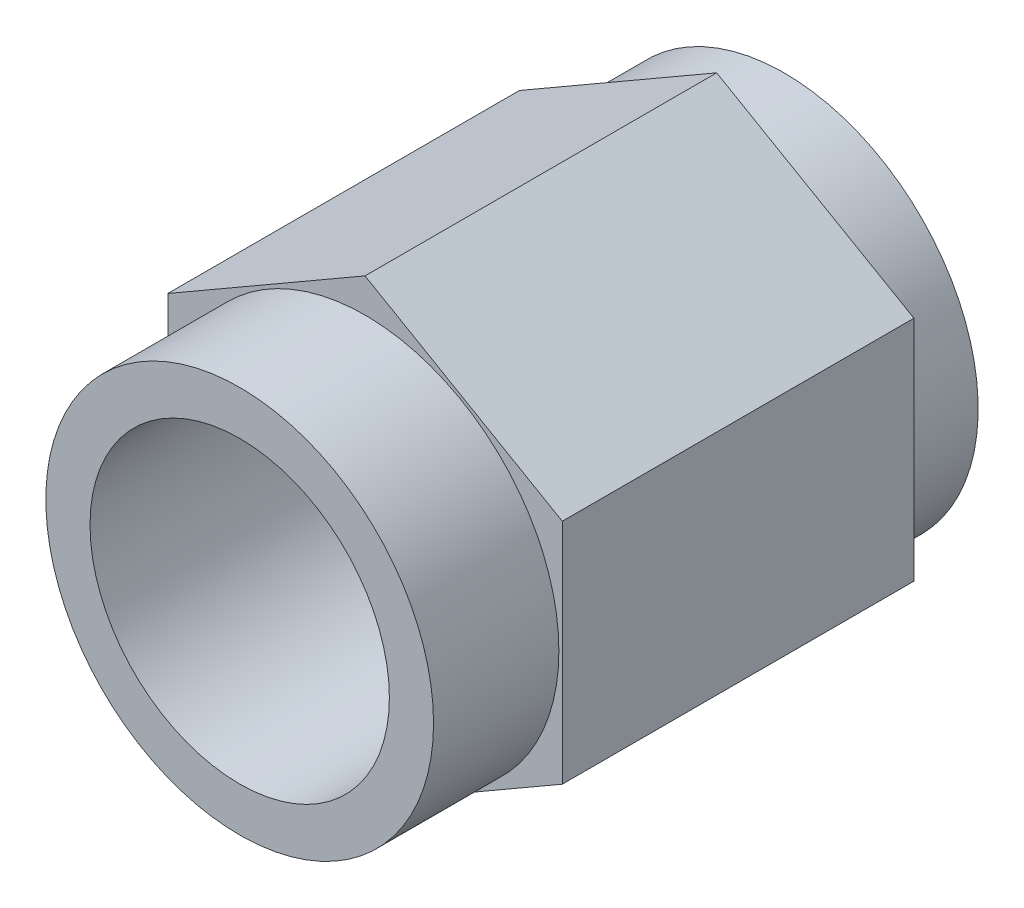
SolidWorks part; units mm, degrees
material "3003 Alloy"
ref_plane "Front Plane" through (0, 0, 0) normal (0, 0, 1) x (1, 0, 0)
ref_plane "Top Plane" through (0, 0, 0) normal (0, 1, 0) x (1, 0, 0)
ref_plane "Right Plane" through (0, 0, 0) normal (1, 0, 0) x (0, 0, -1)
sketch "Sketch1" plane through (0, 0, 0) normal (0, 0, 1) x (1, 0, 0)
  line L0 (0, 0) -> (5.5563, 0) construction
  line L1 (5.5563, -3.2079) -> (5.5563, 3.2079)
  line L2 (5.5563, 3.2079) -> (0, 6.4158)
  line L3 (0, 6.4158) -> (-5.5562, 3.2079)
  line L4 (-5.5562, 3.2079) -> (-5.5562, -3.2079)
  line L5 (-5.5562, -3.2079) -> (0, -6.4158)
  line L6 (0, -6.4158) -> (5.5563, -3.2079)
  circle A0 centre (0, 0) radius 5.5562 construction
  dimension "D1" = 11.1125
extrude "Boss-Extrude1" add sketch "Sketch1" along normal blind 11.811
sketch "Sketch5" plane through (0, 0, 11.811) normal (0, 0, 1) x (1, 0, 0)
  circle A0 centre (0, 0) radius 5.461
  dimension "D1" = 10.922
extrude "Boss-Extrude3" add sketch "Sketch5" along normal blind 3.5306
hole_wizard "3/8-24 Tapped Hole2" positions "Sketch8" profile "Sketch7" tap size "3/8-24" standard "ANSI Inch"
sketch "Sketch8" plane through (0, 0, 15.3416) normal (0, 0, 1) x (1, 0, 0)
  point P0 (0, 0)
sketch "Sketch7" plane through (0, 0, 15.3416) normal (1, 0, 0) x (0, -1, 0)
  line L0 (0, 0) -> (0, 14.5985)
  line L1 (0, 14.5985) -> (4.2164, 12.065)
  line L2 (4.2164, 12.065) -> (4.2164, 0)
  line L5 (4.2164, 0) -> (0, 0)
  line L10 (0, 14.5985) -> (-4.2164, 12.065) construction
  line L11 (0, -6.35) -> (0, 107.95) construction
  dimension "Tap Drill Dia." = 8.4328
  dimension "Tap Drill Depth" = 12.065
  dimension "Drill Angle" = 118
cosmetic thread "Hole Thread2" parameters "D1"=12.065, "D2"=9.525
sketch "Sketch9" plane through (0, 0, 0) normal (0, 0, -1) x (-1, 0, 0)
  circle A0 centre (0, 0) radius 3.0798
  dimension "D1" = 6.1595
extrude "Cut-Extrude1" cut sketch "Sketch9" against normal through all
ref_plane "Plane1" through (0, 0, 5.8166) normal (0, 0, 1) x (1, 0, 0)
sketch "Sketch10" plane through (0, 0, 5.8166) normal (0, 0, 1) x (1, 0, 0)
  circle A0 centre (0, 0) radius 4.1529
  dimension "D1" = 8.3058
extrude "Cut-Extrude2" cut sketch "Sketch10" against normal blind 4.445
sketch "Sketch11" plane through (0, 0, 0) normal (0, 0, -1) x (-1, 0, 0)
  circle A0 centre (0, 0) radius 5.461
  dimension "D1" = 10.922
extrude "Cut-Extrude3" cut sketch "Sketch11" against normal blind 1.905 flip side to cut
